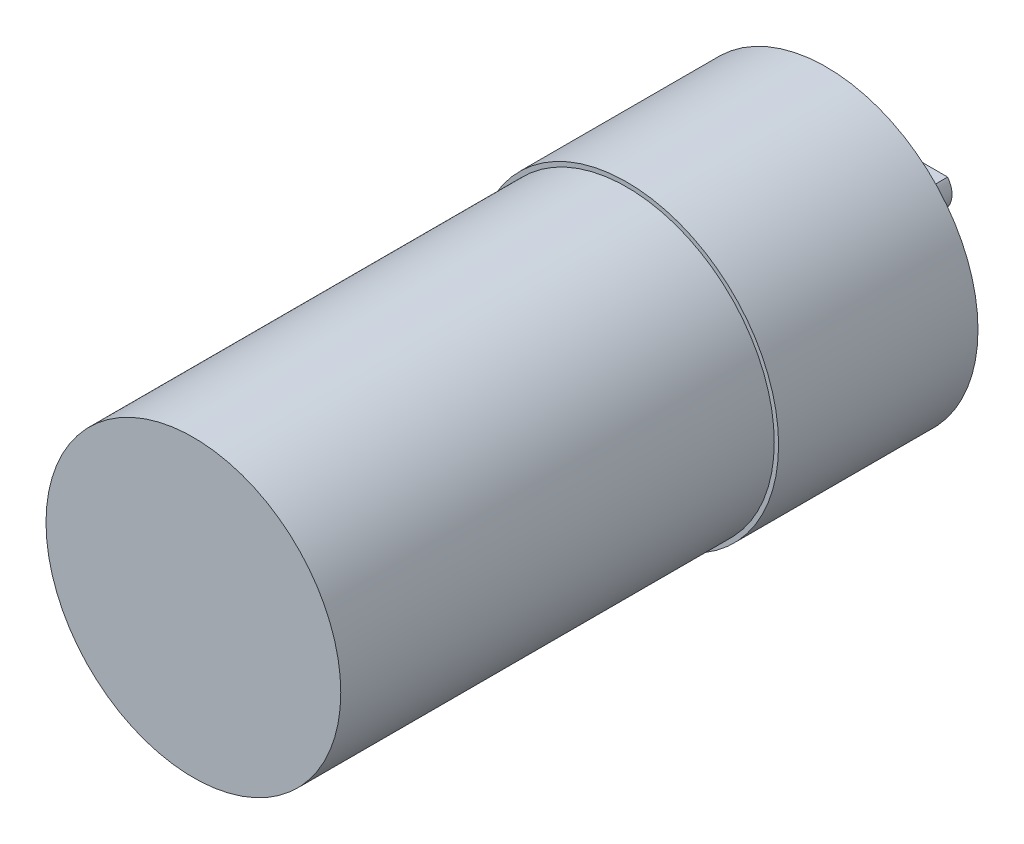
SolidWorks part; units mm, degrees
ref_plane "Front Plane" through (0, 0, 0) normal (0, 0, 1) x (1, 0, 0)
ref_plane "Top Plane" through (0, 0, 0) normal (0, 1, 0) x (1, 0, 0)
ref_plane "Right Plane" through (0, 0, 0) normal (1, 0, 0) x (0, 0, -1)
sketch "Sketch1" plane through (0, 0, 0) normal (0, 0, 1) x (1, 0, 0)
  circle A0 centre (0, 0) radius 17.5
  dimension "D1" = 35
extrude "Boss-Extrude1" add sketch "Sketch1" along normal blind 23
sketch "Sketch2" plane through (0, 0, 23) normal (0, 0, 1) x (1, 0, 0)
  circle A0 centre (0, 0) radius 17
  dimension "D1" = 34
extrude "Boss-Extrude2" add sketch "Sketch2" along normal blind 50
sketch "Sketch3" plane through (0, 0, 0) normal (0, 0, -1) x (-1, 0, 0)
  circle A0 centre (0, 0) radius 5
  dimension "D1" = 10
extrude "Boss-Extrude3" add sketch "Sketch3" along normal blind 2
sketch "Sketch4" plane through (0, 0, -2) normal (0, 0, -1) x (-1, 0, 0)
  line L0 (-2, 1.5) -> (2, 1.5)
  circle A0 centre (0, 0) radius 2.5
  dimension "D1" = 5
  dimension "D2" = 1.5
extrude "Boss-Extrude4" add sketch "Sketch4" along normal blind 10 contours L0 A0
